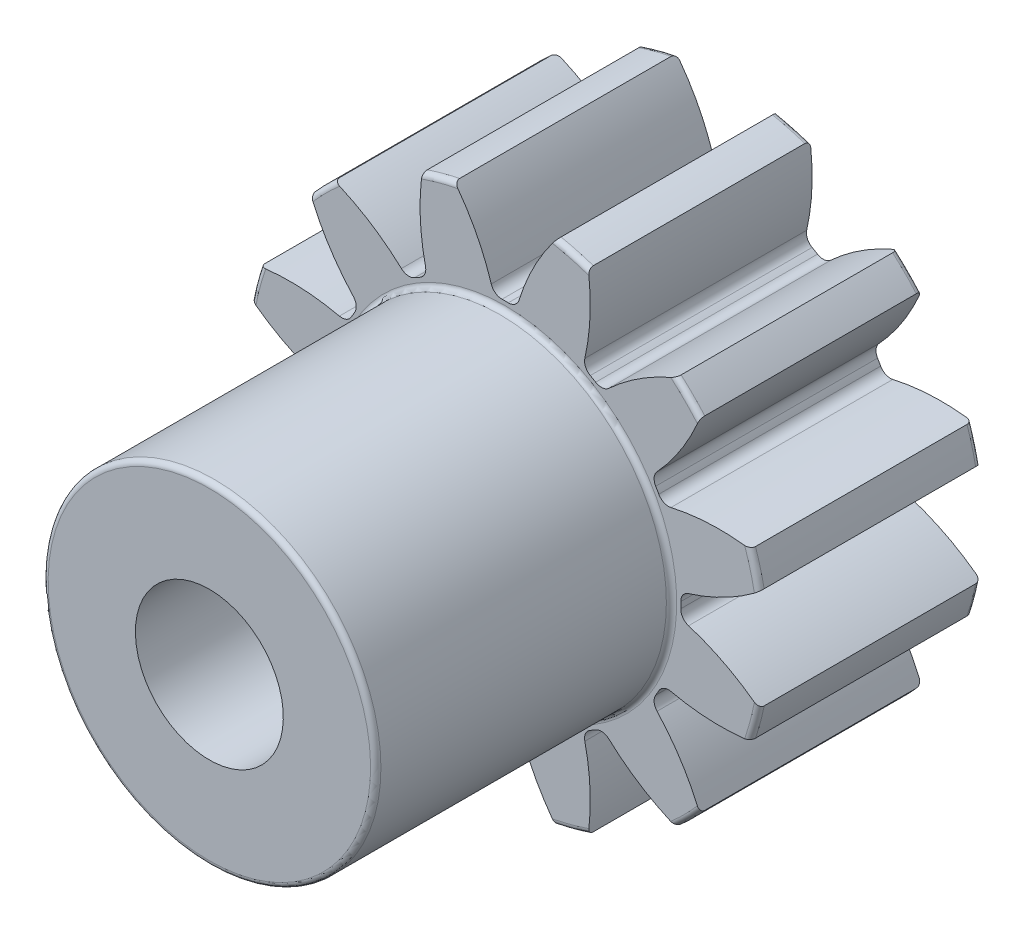
SolidWorks part; units mm, degrees
ref_plane "Front Plane" through (0, 0, 0) normal (0, 0, 1) x (1, 0, 0)
ref_plane "Top Plane" through (0, 0, 0) normal (0, 1, 0) x (1, 0, 0)
ref_plane "Right Plane" through (0, 0, 0) normal (1, 0, 0) x (0, 0, -1)
sketch "Sketch1" plane through (0, 0, 0) normal (0, 0, 1) x (1, 0, 0)
  line L0 (-152.4, 0) -> (152.4, 0) construction
  circle A0 centre (0, 0) radius 3.5 construction
  circle A1 centre (0, 0) radius 3 construction
  circle A2 centre (0, 0) radius 2.375 construction
  circle A3 centre (0, 0) radius 2.25 construction
  circle A4 centre (0, 0) radius 1 construction
  dimension "D2" = 0.5
  dimension "D3" = 1.125
  dimension "D1" = 1.125
sketch "Sketch2" plane through (0, 0, 0) normal (1, 0, 0) x (0, 0, -1)
  line L0 (0, 0) -> (-3, 0) construction
  line L1 (-3, 0) -> (-7, 0) construction
  dimension "Overall Width" = 7
  dimension "Face Width" = 3
sketch "Sketch4" plane through (0, 0, 0) normal (1, 0, 0) x (0, 0, -1)
  line L0 (-7, 1) -> (-7, 2.25)
  line L1 (-7, 2.25) -> (-3, 2.25)
  line L2 (-3, 2.25) -> (-3, 3.5)
  line L3 (-3, 3.5) -> (0, 3.5)
  line L4 (0, 3.5) -> (0, 1)
  line L5 (-3, 2.25) -> (-3, 0) construction
  line L6 (0, 3.5) -> (0, -3.5) construction
  line L7 (-3, 2.25) -> (0, 2.25) construction
  line L12 (-7, 1) -> (0, 1)
revolve "Revolve1" add sketch "Sketch4" angle 360 about L1
fillet "Fillet2" radius 0.07 4 edges at (0, 2.25, 7) (0, 2.25, 3) (0, 3.5, 3) (0, 3.5, 0)
sketch "Sketch7" plane through (0, 0, 3) normal (0, 0, 1) x (1, 0, 0)
  line L0 (0, 0) -> (0, 3.5) construction
  line L1 (0.3916, 2.9743) -> (0.635, 3.4419) construction
  line L3 (0.9059, 3.3807) -> (0.7765, 2.8978) construction
  line L4 (0.7765, 2.8978) -> (0.6147, 2.2941) construction
  line L5 (0, 0) -> (0.6147, 2.2941) construction
  line L6 (0.3916, 2.9743) -> (0, 0) construction
  line L7 (0.3916, 2.9743) -> (0.4568, 3.4701) construction
  line L8 (0.3916, 2.9743) -> (0, 0) construction
  circle A0 centre (0, 0) radius 3.5 construction
  arc A1 (-0.0421, 2.3746) -> (0.0421, 2.3746) centre (0, 0) cw
  circle A2 centre (0, 0) radius 2.375 construction
  arc A3 (-0.3916, 2.9743) -> (0.3916, 2.9743) centre (0, 0) cw construction
  circle A4 centre (0, 0) radius 3 construction
  arc A5 (1.1224, 3.3152) -> (0.6856, 3.4322) centre (0, 0) ccw construction
  arc A6 (0.3916, 2.9743) -> (1.148, 2.7716) centre (0, 0) cw construction
  arc A7 (-0.6856, 3.4322) -> (0.6856, 3.4322) centre (0, 0) cw
  arc A8 (0.188, 2.4801) -> (0.6856, 3.4322) centre (3.0526, 1.5891) cw
  arc A9 (-0.188, 2.4801) -> (-0.6856, 3.4322) centre (-3.0526, 1.5891) ccw
  arc A10 (-0.0421, 2.3746) -> (-0.188, 2.4801) centre (-0.0447, 2.5246) cw
  arc A11 (0.0421, 2.3746) -> (0.188, 2.4801) centre (0.0447, 2.5246) ccw
  point P26 (-0.156, 2.3699)
  point P29 (0.156, 2.3699)
  dimension "D4" = 0.15
  dimension "D5" = 3
  dimension "D3" = 20
  dimension "D1" = 1.5708
  dimension "D2" = 0.7854
extrude "Cut-Extrude2" cut sketch "Sketch7" against normal through all
pattern_circular "CirPattern1" count 12 over 360 about axis through (0, 0, 0) along (0, 0, 1) of "Cut-Extrude2"
equation "\"D1@Sketch1\"=2.25*(\"Pitch Dia.@Sketch1\"/\"Number of Teeth@Sketch1\")"
equation "\"D1@CirPattern1\"=\"Number of Teeth@Sketch1\""
equation "\"D1@Fillet2\"=\"OD@Sketch1\"*.01"
equation "\"D1@Sketch7\"=3.14159*(\"Pitch Dia.@Sketch1\"/\"Number of Teeth@Sketch1\")"
equation "\"D2@Sketch7\"=\"D1@Sketch7\"/2"
equation "\"D4@Sketch7\"=\"D1@Sketch7\"*.0955"
equation "\"D5@Sketch7\"=\"Pitch Dia.@Sketch1\"/2"
